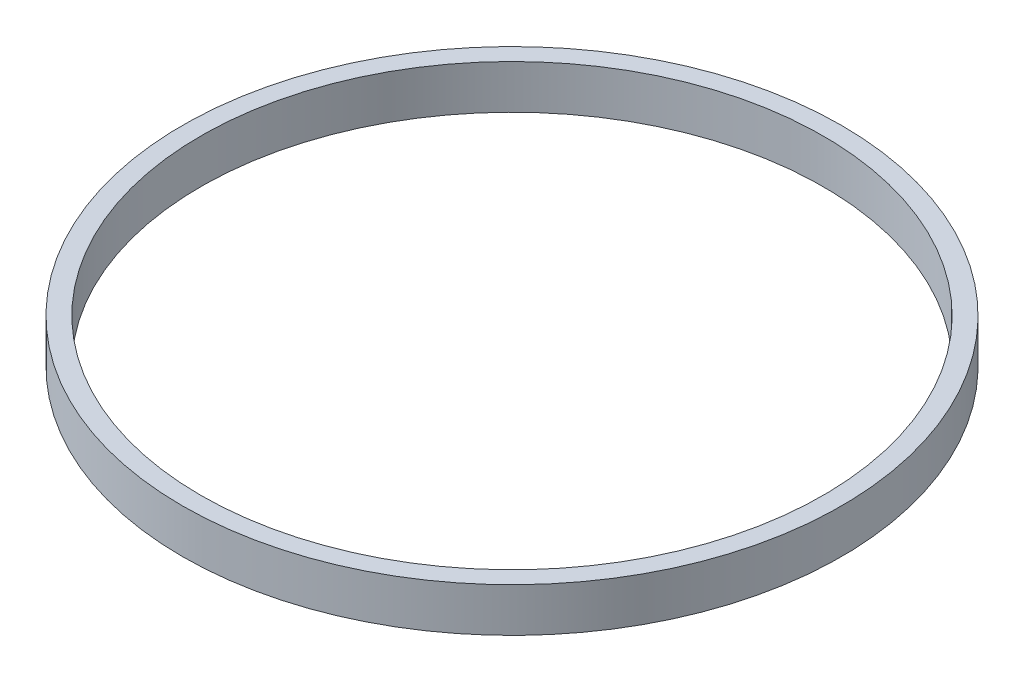
SolidWorks part; units mm, degrees
ref_plane "前视基准面" through (0, 0, 0) normal (0, 0, 1) x (1, 0, 0)
ref_plane "上视基准面" through (0, 0, 0) normal (0, 1, 0) x (1, 0, 0)
ref_plane "右视基准面" through (0, 0, 0) normal (1, 0, 0) x (0, 0, -1)
other "Configuration Table"
sketch "草图1" plane through (0, 0, 0) normal (0, 1, 0) x (1, 0, 0)
  circle A0 centre (0, 0) radius 42.5
  circle A1 centre (0, 0) radius 45
  dimension "D1" = 90
  dimension "D2" = 85
extrude "凸台-拉伸1" add sketch "草图1" along normal blind 6
